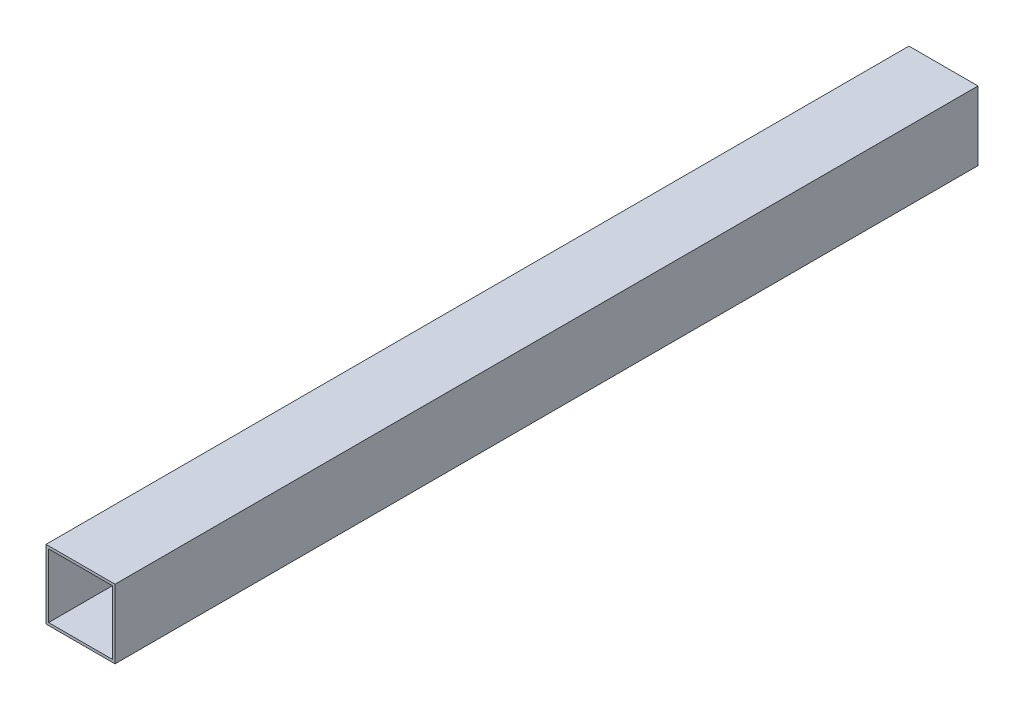
SolidWorks part; units mm, degrees
ref_plane "Plan de face" through (0, 0, 0) normal (0, 0, 1) x (1, 0, 0)
ref_plane "Plan de dessus" through (0, 0, 0) normal (0, 1, 0) x (1, 0, 0)
ref_plane "Plan de droite" through (0, 0, 0) normal (1, 0, 0) x (0, 0, -1)
sketch "Esquisse1" plane through (0, 0, 0) normal (0, 0, 1) x (1, 0, 0)
  line L1 (-20, -20) -> (20, -20)
  line L2 (-20, -20) -> (-20, 20)
  line L3 (-20, 20) -> (20, 20)
  line L4 (20, -20) -> (20, 20)
  line L5 (-20, -20) -> (20, 20) construction
  line L6 (-20, 20) -> (20, -20) construction
  line L7 (-18.5, -18.5) -> (18.5, -18.5)
  line L8 (-18.5, -18.5) -> (-18.5, 18.5)
  line L9 (-18.5, 18.5) -> (18.5, 18.5)
  line L10 (18.5, -18.5) -> (18.5, 18.5)
  line L11 (-18.5, -18.5) -> (18.5, 18.5) construction
  line L12 (-18.5, 18.5) -> (18.5, -18.5) construction
  point P0 (0, 0)
  point P6 (0, 0)
  dimension "D1" = 40
  dimension "D2" = 40
  dimension "D3" = 37
  dimension "D4" = 37
extrude "Boss.-Extru.1" add sketch "Esquisse1" along normal blind 500
